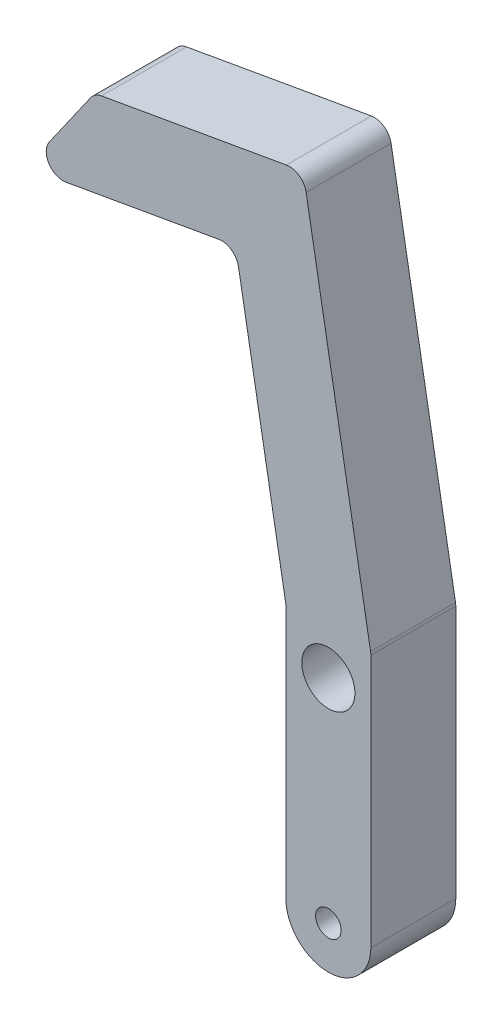
SolidWorks part; units mm, degrees
ref_plane "Front Plane" through (0, 0, 0) normal (0, 0, 1) x (1, 0, 0)
ref_plane "Top Plane" through (0, 0, 0) normal (0, 1, 0) x (1, 0, 0)
ref_plane "Right Plane" through (0, 0, 0) normal (1, 0, 0) x (0, 0, -1)
sketch "Sketch1" plane through (0, 0, 0) normal (0, 0, 1) x (1, 0, 0)
  line L0 (-6.35, -31.75) -> (-6.35, 6.35)
  line L1 (6.35, -31.75) -> (6.35, 6.35)
  line L2 (0, -31.75) -> (0, 6.35) construction
  line L3 (0, 6.35) -> (-8.8213, 56.3782) construction
  line L4 (-8.8213, 56.3782) -> (-46.3425, 49.7622) construction
  line L5 (-6.35, 6.35) -> (-13.8772, 49.0388)
  line L6 (-13.8772, 49.0388) -> (-45.2398, 43.5087)
  line L7 (-45.2398, 43.5087) -> (-34.9381, 58.2211)
  line L8 (-34.9381, 58.2211) -> (-3.7655, 63.7177)
  line L9 (-3.7655, 63.7177) -> (6.35, 6.35)
  line L10 (-45.2398, 43.5087) -> (-46.3425, 49.7622) construction
  circle A0 centre (0, 0) radius 3.9688
  arc A1 (-6.35, -31.75) -> (6.35, -31.75) centre (0, -31.75) ccw
  circle A2 centre (0, -31.75) radius 1.905
  dimension "D1" = 7.9375
  dimension "D2" = 6.35
  dimension "D5" = 3.81
  dimension "D12" = 6.35
  dimension "D13" = 6.35
  dimension "D3" = 6.35
  dimension "D4" = 6.35
  dimension "D6" = 38.1
  dimension "D7" = 170
  dimension "D8" = 50.8
  dimension "D9" = 90
  dimension "D10" = 31.75
  dimension "D11" = 38.1
  dimension "D14" = 45
extrude "Boss-Extrude1" add sketch "Sketch1" along normal blind 12.7
fillet "Fillet1" radius 2.54 6 edges at (-45.2398, 43.5087, 6.35) (-34.9381, 58.2211, 6.35) (-3.7655, 63.7177, 6.35) (6.35, 6.35, 6.35) (-6.35, 6.35, 6.35) (-13.8772, 49.0388, 6.35)
